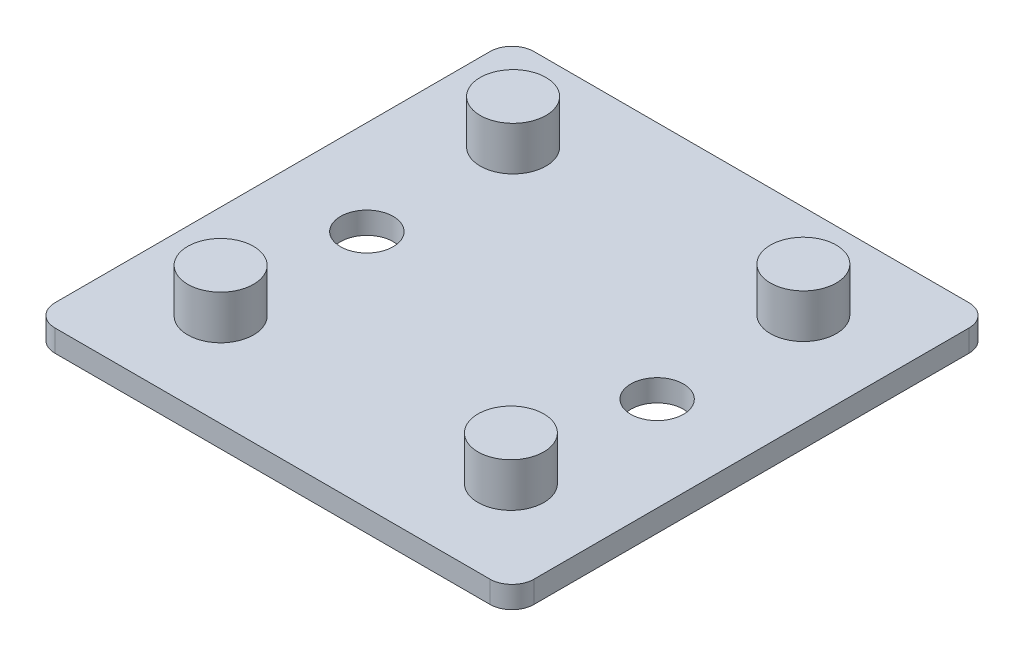
SolidWorks part; units mm, degrees
material "1023 Carbon Steel Sheet (SS)"
ref_plane "Front Plane" through (0, 0, 0) normal (0, 0, 1) x (1, 0, 0)
ref_plane "Top Plane" through (0, 0, 0) normal (0, 1, 0) x (1, 0, 0)
ref_plane "Right Plane" through (0, 0, 0) normal (1, 0, 0) x (0, 0, -1)
sketch "Sketch1" plane through (0, 0, 0) normal (0, 1, 0) x (1, 0, 0)
  line L1 (32.75, -32.75) -> (-32.75, -32.75)
  line L2 (32.75, -32.75) -> (32.75, 32.75)
  line L3 (32.75, 32.75) -> (-32.75, 32.75)
  line L4 (-32.75, -32.75) -> (-32.75, 32.75)
  line L5 (32.75, -32.75) -> (-32.75, 32.75) construction
  line L6 (32.75, 32.75) -> (-32.75, -32.75) construction
  point P0 (0, 0)
  dimension "D1" = 65.5
  dimension "D2" = 65.5
extrude "Boss-Extrude1" add sketch "Sketch1" along normal blind 3
fillet "Fillet1" radius 3 4 edges at (-32.75, 1.5, -32.75) (32.75, 1.5, -32.75) (-32.75, 1.5, 32.75) (32.75, 1.5, 32.75)
sketch "Sketch2" plane through (0, 3, 0) normal (0, 1, 0) x (1, 0, 0)
  line L0 (-29.75, -32.75) -> (29.75, -32.75) construction
  line L1 (32.75, -29.75) -> (32.75, 29.75) construction
  circle A0 centre (19.85, -20) radius 3.6
  circle A1 centre (19.85, 20) radius 3.6
  point P8 (0, 0)
  dimension "D4" = 7.2
  dimension "D5" = 7.2
  dimension "D1" = 12.75
  dimension "D2" = 12.9
  dimension "D3" = 52.75
extrude "Cut-Extrude1" cut sketch "Sketch2" against normal blind 23
mirror "Mirror1" about plane through (0, 0, 0) normal (1, 0, 0) of "Cut-Extrude1"
sketch "Sketch3" plane through (0, 3, 0) normal (0, 1, 0) x (1, 0, 0)
  circle A0 centre (19.85, -20) radius 4.5
  circle A1 centre (19.85, 20) radius 4.5
  circle A2 centre (-19.85, 20) radius 4.5
  circle A3 centre (-19.85, -20) radius 4.5
  circle A4 centre (-19.85, 20) radius 3.6 construction
  circle A5 centre (19.85, 20) radius 3.6 construction
  circle A6 centre (19.85, -20) radius 3.6 construction
  circle A7 centre (-19.85, -20) radius 3.6 construction
  dimension "D1" = 9
extrude "Boss-Extrude2" add sketch "Sketch3" along normal blind 6
sketch "Sketch4" plane through (0, 3, 0) normal (0, 1, 0) x (1, 0, 0)
  line L0 (32.75, -29.75) -> (32.75, 29.75) construction
  circle A0 centre (19.85, 0) radius 3.6
  circle A1 centre (-19.85, 0) radius 3.6
  point P6 (0, 0)
  point P8 (0, 0)
  point P9 (0, 0)
  dimension "D3" = 7.2
  dimension "D4" = 7.2
  dimension "D1" = 12.9
  dimension "D2" = 52.6
extrude "Cut-Extrude2" cut sketch "Sketch4" against normal through all both and the other way through all
